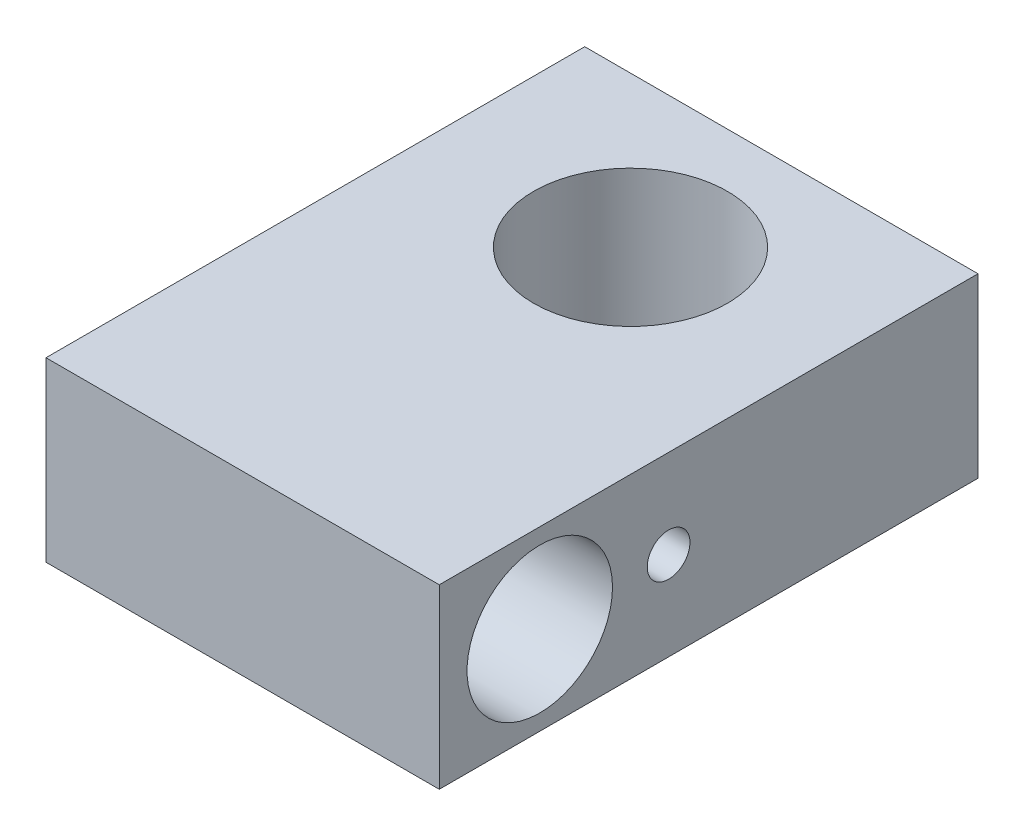
SolidWorks part; units mm, degrees
material "6061-T6 (SS)"
ref_plane "Front Plane" through (0, 0, 0) normal (0, 0, 1) x (1, 0, 0)
ref_plane "Top Plane" through (0, 0, 0) normal (0, 1, 0) x (1, 0, 0)
ref_plane "Right Plane" through (0, 0, 0) normal (1, 0, 0) x (0, 0, -1)
sketch "Sketch1" plane through (0, 0, 0) normal (0, 1, 0) x (1, 0, 0)
  line L0 (9.125, 7) -> (9.125, -18)
  line L1 (9.125, -18) -> (-9.125, -18)
  line L2 (-9.125, -18) -> (-9.125, 7)
  line L4 (-9.125, 7) -> (9.125, 7)
  line L8 (0, 0) -> (0, 7) construction
  point P4 (9.125, -18)
  point P6 (-9.125, -18)
  point P11 (-9.125, 7)
  point P12 (9.125, 7)
  dimension "D1" = 7
  dimension "D2" = 25
  dimension "D3" = 18.25
extrude "Boss-Extrude1" add sketch "Sketch1" along normal blind 8.22
hole_wizard "M10x1.0 Tapped Hole1" positions "Sketch3" profile "Sketch2" tap size "M10x1.0" standard "Ansi Metric" end condition through all
sketch "Sketch3" plane through (0, 8.22, 0) normal (0, 1, 0) x (-1, 0, 0)
  point P0 (0, 0)
sketch "Sketch2" plane through (0, 8.22, 0) normal (1, 0, 0) x (0, 0, 1)
  line L0 (0, 0) -> (0, 8.22)
  line L1 (0, 8.22) -> (4.5, 8.22)
  line L2 (4.5, 8.22) -> (4.5, 0)
  line L5 (4.5, 0) -> (0, 0)
  line L11 (0, -6.35) -> (0, 107.95) construction
  dimension "Thru Tap Drill Dia." = 9
  dimension "Thru Tap Drill Depth" = 8.22
cosmetic thread "Hole Thread1" parameters "D2"=10
sketch "Sketch7" plane through (9.125, 0, 0) normal (1, 0, 0) x (0, 0, -1)
  line L0 (-18, 4.11) -> (-13.3362, 4.11) construction
  line L1 (-18, 8.22) -> (-18, 0) construction
  circle A0 centre (-13.3362, 4.11) radius 3.375
  circle A1 centre (-7.3575, 4.11) radius 0.9906
  dimension "D1" = 6.75
  dimension "D3" = 1.9812
  dimension "D4" = 7.3575
  dimension "D5" = 13.3362
extrude "Cut-Extrude2" cut sketch "Sketch7" against normal through all
